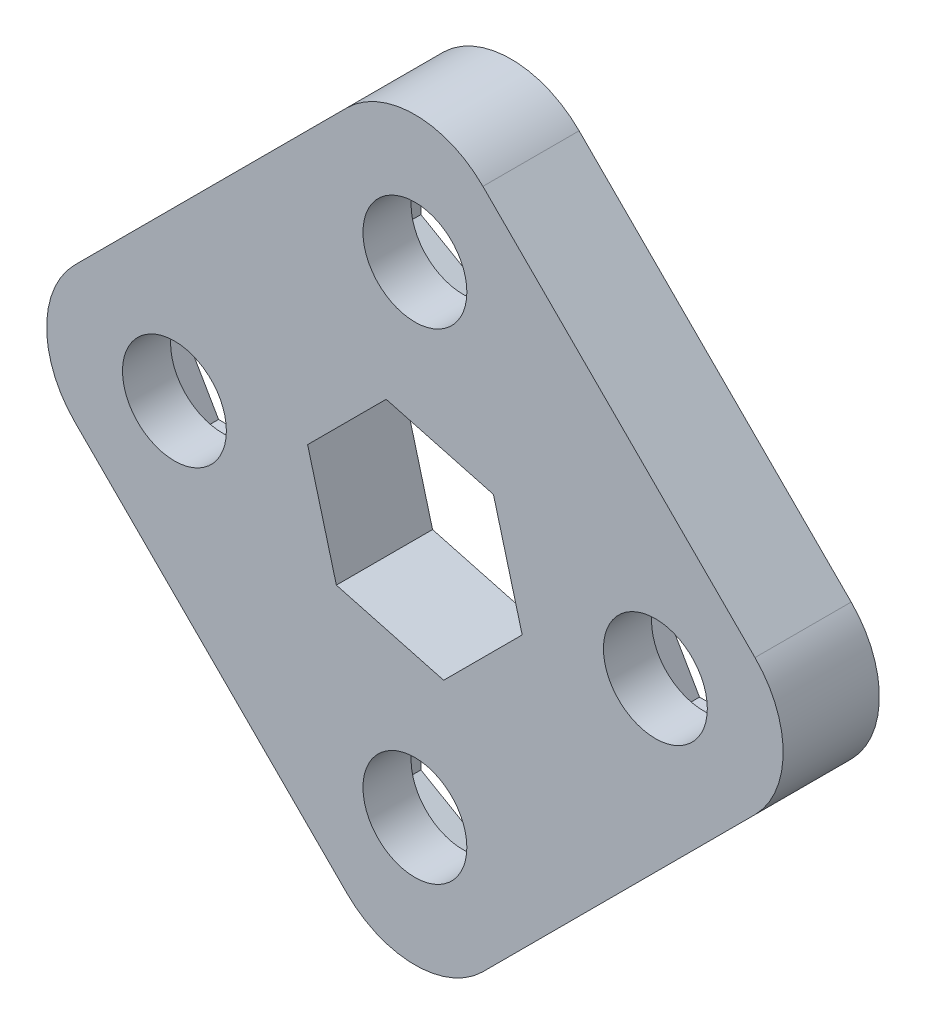
SolidWorks part; units mm, degrees
ref_plane "Front Plane" through (0, 0, 0) normal (0, 0, 1) x (1, 0, 0)
ref_plane "Top Plane" through (0, 0, 0) normal (0, 1, 0) x (1, 0, 0)
ref_plane "Right Plane" through (0, 0, 0) normal (1, 0, 0) x (0, 0, -1)
sketch "Sketch2" plane through (0, 0, 0) normal (0, 0, 1) x (1, 0, 0)
  line L0 (0, -29.6348) -> (0, 29.6348) construction
  line L1 (5.1848, 5.1848) -> (-1.8978, 7.0825)
  line L2 (-1.8978, 7.0825) -> (-7.0825, 1.8978)
  line L3 (-7.0825, 1.8978) -> (-5.1848, -5.1848)
  line L4 (-5.1848, -5.1848) -> (1.8978, -7.0825)
  line L5 (1.8978, -7.0825) -> (7.0825, -1.8978)
  line L6 (7.0825, -1.8978) -> (5.1848, 5.1848)
  line L7 (0, 0) -> (0, 15.875) construction
  line L8 (-4.4901, 22.4506) -> (-22.4506, 4.4901)
  line L9 (29.6348, 0) -> (-29.6348, 0) construction
  line L10 (-22.4506, -4.4901) -> (-4.4901, -22.4506)
  line L11 (4.4901, -22.4506) -> (22.4506, -4.4901)
  line L12 (22.4506, 4.4901) -> (4.4901, 22.4506)
  line L13 (0, 26.9408) -> (0, -26.9408) construction
  line L14 (-26.9408, 0) -> (26.9408, 0) construction
  circle A0 centre (0, 0) radius 6.35 construction
  circle A1 centre (0, 15.875) radius 3.429
  circle A2 centre (15.875, 0) radius 3.429
  circle A3 centre (0, -15.875) radius 3.429
  circle A4 centre (-15.875, 0) radius 3.429
  circle A6 centre (0, 0) radius 15.875 construction
  arc A7 (-22.4506, 4.4901) -> (-22.4506, -4.4901) centre (-17.9605, 0) ccw
  arc A8 (-4.4901, -22.4506) -> (4.4901, -22.4506) centre (0, -17.9605) ccw
  arc A9 (22.4506, -4.4901) -> (22.4506, 4.4901) centre (17.9605, 0) ccw
  arc A10 (4.4901, 22.4506) -> (-4.4901, 22.4506) centre (0, 17.9605) ccw
  point P14 (0, 0)
  dimension "D1" = 12.7
  dimension "D3" = 15.875
  dimension "D4" = 6.858
  dimension "D6" = 38.1
  dimension "D7" = 6.35
  dimension "D5" = 4
extrude "Boss-Extrude1" add sketch "Sketch2" along normal blind 6.35
sketch "Sketch3" plane through (0, 0, 0) normal (0, 0, -1) x (-1, 0, 0)
  line L0 (0, 3.4925) -> (0, -3.4925) construction
  line L1 (5.9531, 19.312) -> (0, 22.7491)
  line L2 (0, 22.7491) -> (-5.9531, 19.312)
  line L3 (-5.9531, 19.312) -> (-5.9531, 12.438)
  line L4 (-5.9531, 12.438) -> (0, 9.0009)
  line L5 (0, 9.0009) -> (5.9531, 12.438)
  line L6 (5.9531, 12.438) -> (5.9531, 19.312)
  line L7 (12.438, -5.9531) -> (19.312, -5.9531)
  line L8 (9.0009, 0) -> (12.438, -5.9531)
  line L9 (12.438, 5.9531) -> (9.0009, 0)
  line L10 (19.312, 5.9531) -> (12.438, 5.9531)
  line L11 (22.7491, 0) -> (19.312, 5.9531)
  line L12 (19.312, -5.9531) -> (22.7491, 0)
  line L13 (-5.9531, -12.438) -> (-5.9531, -19.312)
  line L14 (0, -9.0009) -> (-5.9531, -12.438)
  line L15 (5.9531, -12.438) -> (0, -9.0009)
  line L16 (5.9531, -19.312) -> (5.9531, -12.438)
  line L17 (0, -22.7491) -> (5.9531, -19.312)
  line L18 (-5.9531, -19.312) -> (0, -22.7491)
  line L19 (-12.438, 5.9531) -> (-19.312, 5.9531)
  line L20 (-9.0009, 0) -> (-12.438, 5.9531)
  line L21 (-12.438, -5.9531) -> (-9.0009, 0)
  line L22 (-19.312, -5.9531) -> (-12.438, -5.9531)
  line L23 (-22.7491, 0) -> (-19.312, -5.9531)
  line L24 (-19.312, 5.9531) -> (-22.7491, 0)
  line L25 (0, 0) -> (0, 9.0009) construction
  line L26 (0, 0) -> (9.0009, 0) construction
  line L27 (3.4925, 0) -> (-3.4925, 0) construction
  circle A0 centre (0, 15.875) radius 5.9531 construction
  circle A1 centre (15.875, 0) radius 5.9531 construction
  circle A2 centre (0, -15.875) radius 5.9531 construction
  circle A3 centre (-15.875, 0) radius 5.9531 construction
  point P12 (0, 0)
  point P13 (11.4769, 3.4952)
  point P18 (0, 0)
  dimension "D1" = 11.9062
  dimension "D3" = 90
  dimension "D4" = 9.0009
  dimension "D2" = 4
extrude "Cut-Extrude1" cut sketch "Sketch3" against normal blind 3.175
